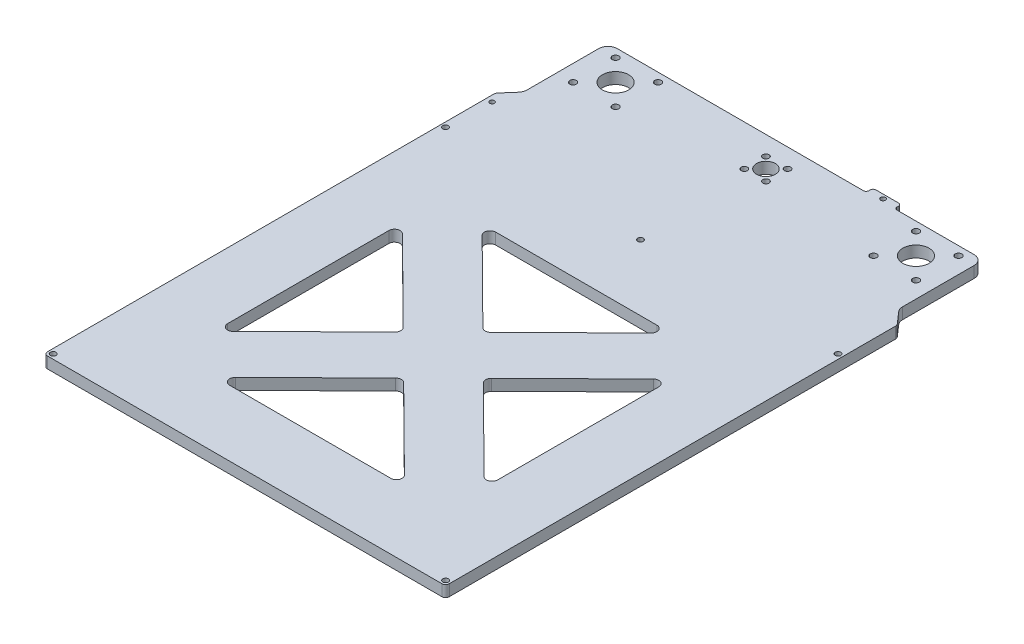
SolidWorks part; units mm, degrees
ref_plane "Спереди" through (0, 0, 0) normal (0, 0, 1) x (1, 0, 0)
ref_plane "Сверху" through (0, 0, 0) normal (0, 1, 0) x (1, 0, 0)
ref_plane "Справа" through (0, 0, 0) normal (1, 0, 0) x (0, 0, -1)
sketch "Эскиз1" plane through (0, 0, 0) normal (0, 1, 0) x (1, 0, 0)
  line L0 (96.263, 98.0685) -> (96.263, 136.1921)
  line L1 (91.263, 141.1921) -> (50.263, 141.1921)
  line L2 (48.763, 142.6921) -> (48.763, 143.3921)
  line L3 (47.263, 144.8921) -> (35.263, 144.8921)
  line L4 (33.763, 143.3921) -> (33.763, 142.6921)
  line L5 (32.263, 141.1921) -> (-98.737, 141.1921)
  line L6 (-103.737, 136.1921) -> (-103.737, 108.9921)
  line L7 (-103.737, 102.4921) -> (-103.737, 98.0685)
  line L8 (-104.9715, 94.7789) -> (-110.2141, 88.7777)
  line L9 (-110.7079, 87.4619) -> (-110.7079, -150.3079)
  line L10 (-108.7079, -152.3079) -> (101.2921, -152.3079)
  line L11 (103.2921, -150.3079) -> (103.2921, 87.3955)
  line L12 (102.7983, 88.7113) -> (97.4975, 94.7789)
  line L13 (-46.5243, 24.1921) -> (39.3063, 24.1921)
  line L14 (-75.7079, -3.5434) -> (-75.7079, -89.3741)
  line L15 (-46.7222, -117.3079) -> (39.1084, -117.3079)
  line L16 (68.2921, -3.7418) -> (68.2921, -89.5725)
  line L17 (-5.8379, -69.7369) -> (-48.8297, -112.1729)
  line L18 (-70.5967, -1.4121) -> (-27.1967, -44.4038)
  line L19 (-48.6356, 19.0607) -> (-5.7967, -23.3752)
  line L20 (-70.6005, -91.5091) -> (-27.2005, -48.6702)
  line L21 (63.1846, -1.6067) -> (19.7846, -44.4456)
  line L22 (-1.5779, -23.3789) -> (41.4138, 19.057)
  line L23 (19.7808, -48.712) -> (63.1808, -91.7038)
  line L24 (-1.6192, -69.7407) -> (41.2197, -112.1766)
  line L25 (-103.737, 108.9921) -> (-103.737, 102.4921)
  line L26 (-108.2079, 59.1921) -> (96.7752, 59.1921) construction
  line L27 (100.7921, -149.8079) -> (100.7921, 62.2793) construction
  line L28 (96.7752, 59.1921) -> (101.464, 59.1921) construction
  circle A0 centre (-107.4856, 83.2466) radius 1.25
  circle A1 centre (-108.2079, -149.8079) radius 1.5
  circle A2 centre (100.7921, -149.8079) radius 1.5
  circle A3 centre (2.0421, 131.0421) radius 1.65
  circle A4 centre (-9.4579, 131.0421) radius 1.65
  circle A5 centre (-4.4303, 59.1921) radius 1.5
  circle A6 centre (-3.7079, 125.2921) radius 5
  circle A7 centre (-72.3942, 113.8784) radius 1.75
  circle A8 centre (-95.0216, 136.5058) radius 1.75
  circle A9 centre (-83.7079, 125.1921) radius 7
  circle A10 centre (-72.3942, 136.5058) radius 1.75
  circle A11 centre (-95.0216, 113.8784) radius 1.75
  circle A12 centre (87.6058, 136.5058) radius 1.75
  circle A13 centre (76.2921, 125.1921) radius 7
  circle A14 centre (64.9784, 136.5058) radius 1.75
  circle A15 centre (87.6058, 113.8784) radius 1.75
  circle A16 centre (-9.4579, 119.5421) radius 1.65
  circle A17 centre (2.0421, 119.5421) radius 1.65
  circle A18 centre (41.2921, 142.6921) radius 1.3
  circle A19 centre (64.9784, 113.8784) radius 1.75
  arc A20 (96.263, 136.1921) -> (91.263, 141.1921) centre (91.263, 136.1921) ccw
  arc A21 (48.763, 142.6921) -> (50.263, 141.1921) centre (50.263, 142.6921) ccw
  arc A22 (48.763, 143.3921) -> (47.263, 144.8921) centre (47.263, 143.3921) ccw
  arc A23 (35.263, 144.8921) -> (33.763, 143.3921) centre (35.263, 143.3921) ccw
  arc A24 (32.263, 141.1921) -> (33.763, 142.6921) centre (32.263, 142.6921) ccw
  arc A25 (-98.737, 141.1921) -> (-103.737, 136.1921) centre (-98.737, 136.1921) ccw
  arc A26 (-104.9715, 94.7789) -> (-103.737, 98.0685) centre (-108.737, 98.0685) ccw
  arc A27 (-110.2141, 88.7777) -> (-110.7079, 87.4619) centre (-108.7079, 87.4619) ccw
  arc A28 (-110.7079, -150.3079) -> (-108.7079, -152.3079) centre (-108.7079, -150.3079) ccw
  arc A29 (101.2921, -152.3079) -> (103.2921, -150.3079) centre (101.2921, -150.3079) ccw
  arc A30 (103.2921, 87.3955) -> (102.7983, 88.7113) centre (101.2921, 87.3955) ccw
  arc A31 (96.263, 98.0685) -> (97.4975, 94.7789) centre (101.263, 98.0685) ccw
  arc A32 (-46.5243, 24.1921) -> (-48.6356, 19.0607) centre (-46.5243, 21.1921) ccw
  arc A33 (41.4138, 19.057) -> (39.3063, 24.1921) centre (39.3063, 21.1921) ccw
  arc A34 (68.2921, -3.7418) -> (63.1846, -1.6067) centre (65.2921, -3.7418) ccw
  arc A35 (63.1808, -91.7038) -> (68.2921, -89.5725) centre (65.2921, -89.5725) ccw
  arc A36 (39.1084, -117.3079) -> (41.2197, -112.1766) centre (39.1084, -114.3079) ccw
  arc A37 (-48.8297, -112.1729) -> (-46.7222, -117.3079) centre (-46.7222, -114.3079) ccw
  arc A38 (-5.7967, -23.3752) -> (-1.5779, -23.3789) centre (-3.6854, -21.2439) ccw
  arc A39 (19.7846, -44.4456) -> (19.7808, -48.712) centre (21.8921, -46.5807) ccw
  arc A40 (-1.6192, -69.7407) -> (-5.8379, -69.7369) centre (-3.7305, -71.872) ccw
  arc A41 (-27.2005, -48.6702) -> (-27.1967, -44.4038) centre (-29.3079, -46.5351) ccw
  arc A42 (-70.5967, -1.4121) -> (-75.7079, -3.5434) centre (-72.7079, -3.5434) ccw
  arc A43 (-75.7079, -89.3741) -> (-70.6005, -91.5091) centre (-72.7079, -89.3741) ccw
  circle A44 centre (100.7921, 59.1921) radius 1.5
  circle A45 centre (-108.2079, 59.1921) radius 1.5
  dimension "D1" = 80
  dimension "D2" = 80
  dimension "D6" = 3
  dimension "D7" = 3
  dimension "D9" = 2.5
  dimension "D10" = 2.5
  dimension "D11" = 209
  dimension "D12" = 209
  dimension "D13" = 209
  dimension "D3" = 16
  dimension "D4" = 15.9
  dimension "D5" = 16
  dimension "D8" = 209
extrude "Бобышка-Вытянуть1" add sketch "Эскиз1" along normal blind 6
